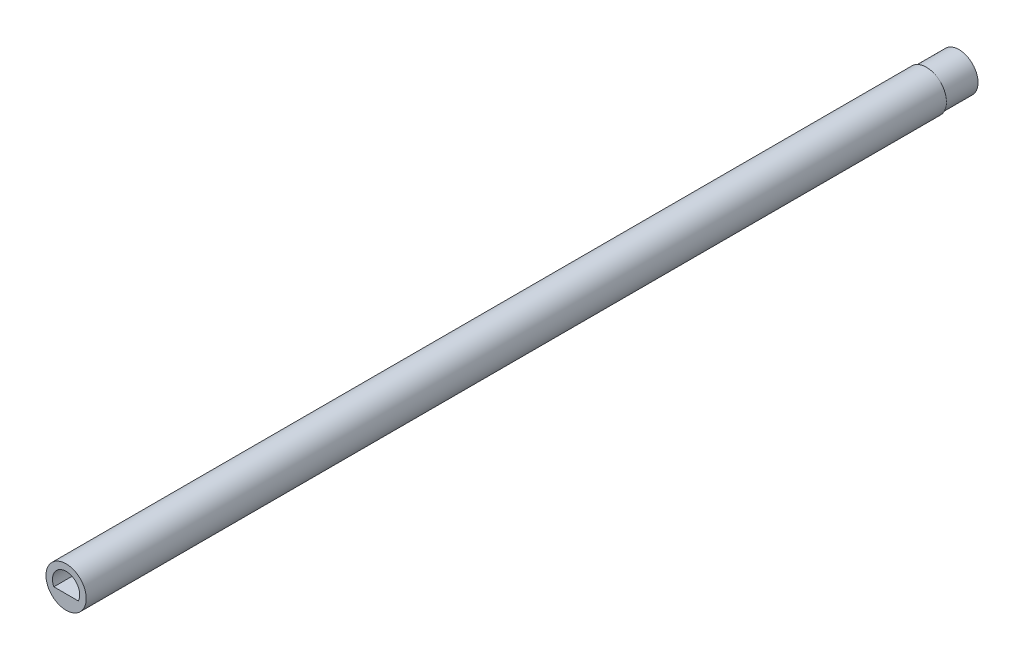
SolidWorks part; units mm, degrees
ref_plane "Front Plane" through (0, 0, 0) normal (0, 0, 1) x (1, 0, 0)
ref_plane "Top Plane" through (0, 0, 0) normal (0, 1, 0) x (1, 0, 0)
ref_plane "Right Plane" through (0, 0, 0) normal (1, 0, 0) x (0, 0, -1)
sketch "Sketch1" plane through (0, 0, 0) normal (0, 0, 1) x (1, 0, 0)
  circle A0 centre (0, 0) radius 3.7
  dimension "D1" = 7.4
extrude "Boss-Extrude1" add sketch "Sketch1" along normal blind 158
sketch "Sketch2" plane through (0, 0, 0) normal (0, 0, -1) x (-1, 0, 0)
  circle A0 centre (0, 0) radius 3.5
  dimension "D1" = 7
extrude "Boss-Extrude2" add sketch "Sketch2" along normal blind 6
sketch "Sketch4" plane through (0, 0, 158) normal (0, 0, 1) x (1, 0, 0)
  line L0 (0, 0.6221) -> (0, -2.2926) construction
  line L1 (-2.25, -1.0897) -> (2.25, -1.0897)
  arc A0 (-2.25, -1.0897) -> (2.25, -1.0897) centre (0, 0) cw
  dimension "D1" = 2.5
  dimension "D2" = 4.5
  dimension "D3" = 2.25
extrude "Cut-Extrude1" cut sketch "Sketch4" against normal blind 10
